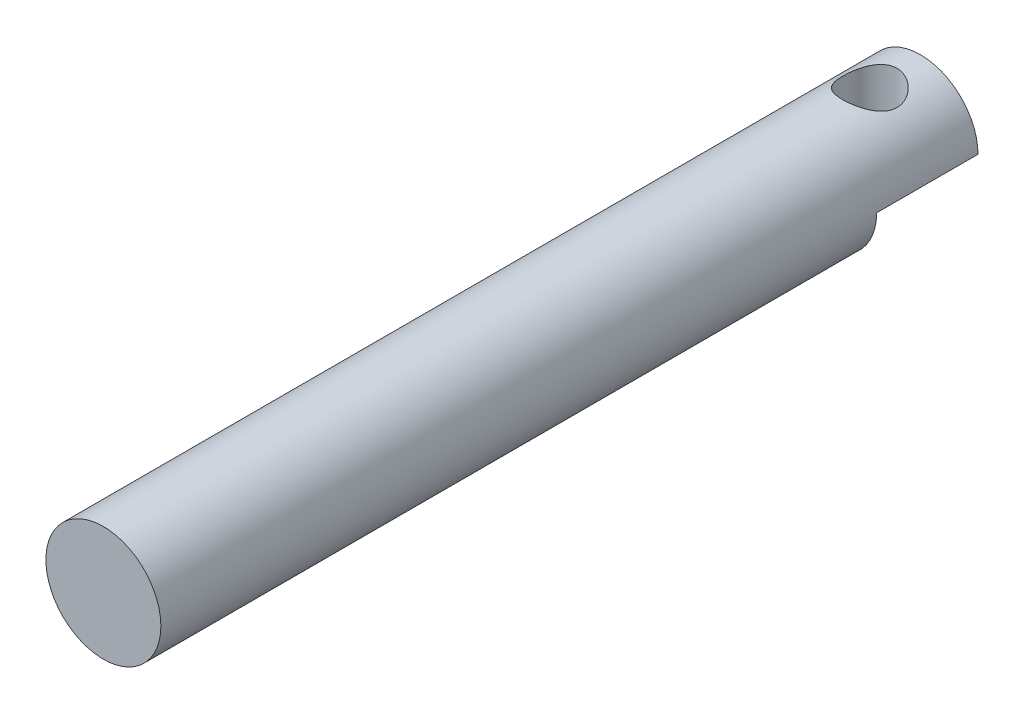
SolidWorks part; units mm, degrees
ref_plane "Front Plane" through (0, 0, 0) normal (0, 0, 1) x (1, 0, 0)
ref_plane "Top Plane" through (0, 0, 0) normal (0, 1, 0) x (1, 0, 0)
ref_plane "Right Plane" through (0, 0, 0) normal (1, 0, 0) x (0, 0, -1)
sketch "Sketch1" plane through (0, 0, 0) normal (0, 0, 1) x (1, 0, 0)
  circle A0 centre (0, 0) radius 3.175
  dimension "D1" = 6.35
extrude "Boss-Extrude1" add sketch "Sketch1" along normal blind 45.12
sketch "Sketch2" plane through (0, 0, 0) normal (0, 1, 0) x (1, 0, 0)
  line L0 (3.175, -45.12) -> (3.175, 0) construction
  line L1 (-3.175, 0) -> (3.175, 0)
  line L2 (-3.175, 0) -> (-3.175, -5.5973)
  line L3 (-3.175, -5.5973) -> (3.175, -5.5973)
  line L4 (3.175, 0) -> (3.175, -5.5973)
extrude "Cut-Extrude1" cut sketch "Sketch2" against normal blind 7
sketch "Sketch3" plane through (0, 0, 0) normal (0, -1, 0) x (1, 0, 0)
  line L1 (-3.175, 0) -> (-3.175, 5.5973) construction
  circle A0 centre (0, 2.7986) radius 1.5
  point P9 (-3.175, 2.7986)
  dimension "D1" = 3
extrude "Cut-Extrude2" cut sketch "Sketch3" against normal blind 7
